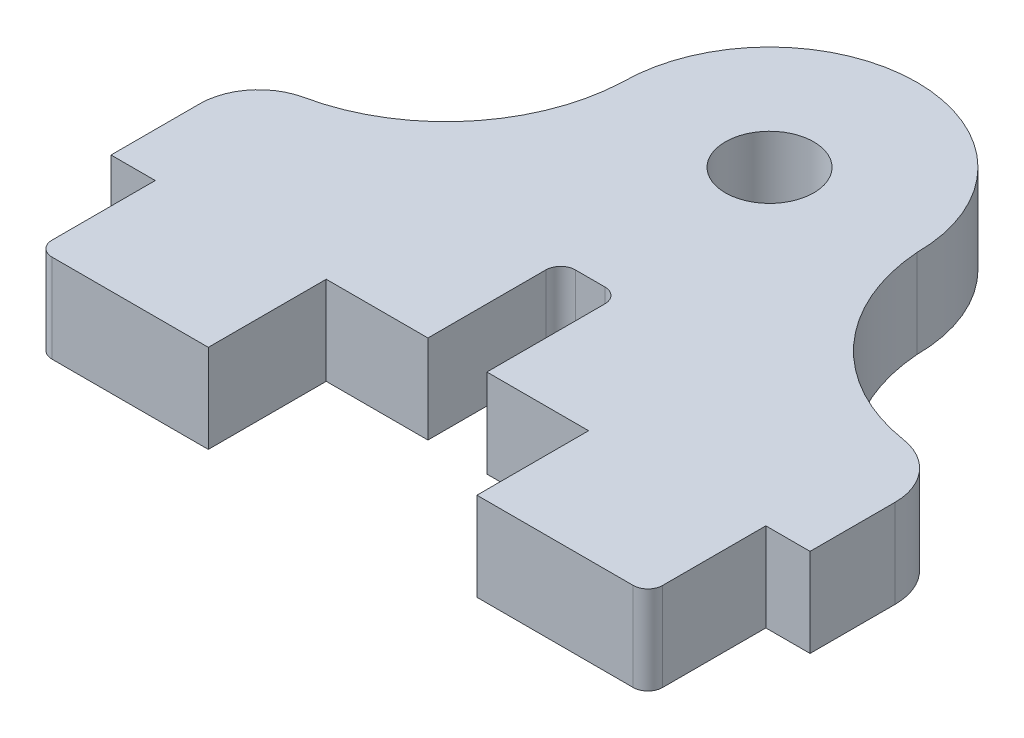
SolidWorks part; units mm, degrees
ref_plane "Front Plane" through (0, 0, 0) normal (0, 0, 1) x (1, 0, 0)
ref_plane "Top Plane" through (0, 0, 0) normal (0, 1, 0) x (1, 0, 0)
ref_plane "Right Plane" through (0, 0, 0) normal (1, 0, 0) x (0, 0, -1)
sketch "Sketch2" plane through (0, 0, 0) normal (0, 1, 0) x (1, 0, 0)
  line L1 (-11.5314, -10.8064) -> (-10.0314, -10.8064)
  line L2 (-10.0314, -10.8064) -> (-10.0314, -14.8064)
  line L3 (-10.0314, -14.8064) -> (-4.2314, -14.8064)
  line L5 (-11.5314, -10.8064) -> (-11.5314, -5.9738)
  line L7 (11.9686, -5.7619) -> (11.9686, -10.5944)
  line L8 (-4.2314, -14.8064) -> (-4.2314, -10.8064)
  line L9 (11.9686, -10.5944) -> (10.4686, -10.5944)
  line L10 (10.4686, -10.5944) -> (10.4686, -14.5944)
  line L11 (10.4686, -14.5944) -> (4.6686, -14.5944)
  line L12 (4.6686, -14.5944) -> (4.6686, -10.8064)
  line L13 (-4.2314, -10.8064) -> (-0.7814, -10.8064)
  line L16 (-0.7814, -10.8064) -> (-0.7814, -6.3064)
  line L17 (-0.7814, -6.3064) -> (1.2186, -6.3064)
  line L18 (1.2186, -6.3064) -> (1.2186, -10.8064)
  line L19 (1.2186, -10.8064) -> (4.6686, -10.8064)
  arc A0 (5, 0) -> (-5, 0) centre (0, 0) ccw
  arc A2 (-11.5314, -5.9738) -> (-5, 0) centre (-11.2526, 0.2788) ccw
  arc A3 (5, 0) -> (11.9686, -5.7619) centre (11.2434, 0.456) ccw
  point P10 (0, 0)
  dimension "D1" = 10
  dimension "D11" = 23.5
  dimension "D2" = 4
  dimension "D3" = 1.5
  dimension "D5" = 5.8
  dimension "D6" = 1.5
  dimension "D7" = 4
  dimension "D8" = 5.8
  dimension "D9" = 2
  dimension "D10" = 4.5
extrude "Boss-Extrude1" add sketch "Sketch2" along normal blind 3
sketch "Sketch3" plane through (0, 3, 0) normal (0, 1, 0) x (1, 0, 0)
  circle A0 centre (0, 0) radius 1.5
  dimension "D1" = 3
extrude "Cut-Extrude1" cut sketch "Sketch3" against normal blind 3
fillet "Fillet1" radius 2 2 edges at (-11.5314, 1.5, 5.9738) (11.9686, 1.5, 5.7619)
fillet "Fillet2" radius 0.5 4 edges at (10.4686, 1.5, 14.5944) (1.2186, 1.5, 6.3064) (-0.7814, 1.5, 6.3064) (-10.0314, 1.5, 14.8064)
